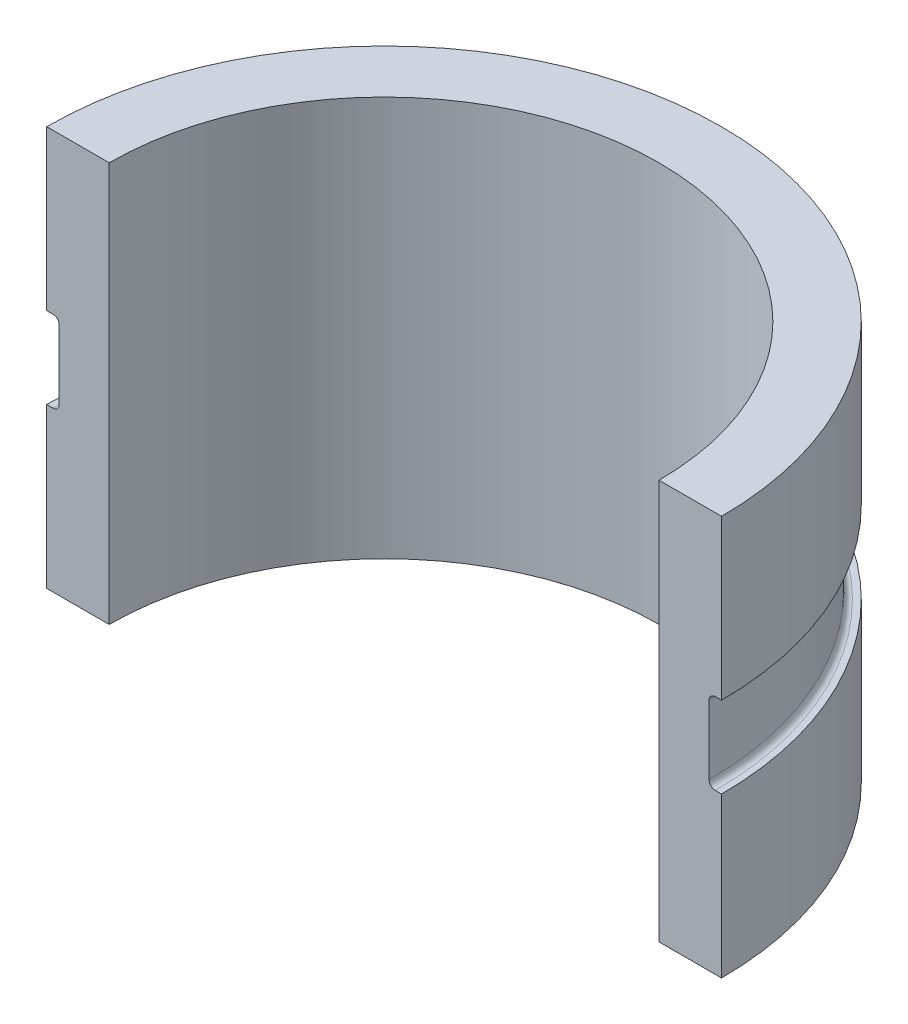
SolidWorks part; units mm, degrees
ref_plane "Front Plane" through (0, 0, 0) normal (0, 0, 1) x (1, 0, 0)
ref_plane "Top Plane" through (0, 0, 0) normal (0, 1, 0) x (1, 0, 0)
ref_plane "Right Plane" through (0, 0, 0) normal (1, 0, 0) x (0, 0, -1)
sketch "Sketch1" plane through (0, 0, 0) normal (0, 1, 0) x (1, 0, 0)
  line L0 (-68.58, 0) -> (-55.88, 0)
  line L1 (55.88, 0) -> (68.58, 0)
  arc A0 (-55.88, 0) -> (55.88, 0) centre (0, 0) cw
  arc A1 (-68.58, 0) -> (68.58, 0) centre (0, 0) cw
  dimension "D1" = 55.88
  dimension "D2" = 68.58
extrude "Boss-Extrude1" add sketch "Sketch1" along normal blind 81.28
ref_axis "Axis1" through (0, 81.28, 0) along (0, -1, 0)
sketch "Sketch2" plane through (0, 0, 0) normal (0, 0, 1) x (1, 0, 0)
  line L0 (-68.58, 48.895) -> (-66.04, 48.895)
  line L1 (-68.58, 81.28) -> (-68.58, 0) construction
  line L2 (-66.04, 48.895) -> (-66.04, 32.385)
  line L3 (-66.04, 32.385) -> (-68.58, 32.385)
  line L4 (-68.58, 32.385) -> (-68.58, 48.895)
  point P5 (-68.58, 40.64)
  dimension "D1" = 2.54
  dimension "D2" = 16.51
revolve "Cut-Revolve1" cut sketch "Sketch2" angle 180 about axis through (0, 81.28, 0) along (0, -1, 0)
fillet "Fillet1" radius 1.27 2 edges at (0, 48.895, -66.04) (0, 32.385, -66.04)
